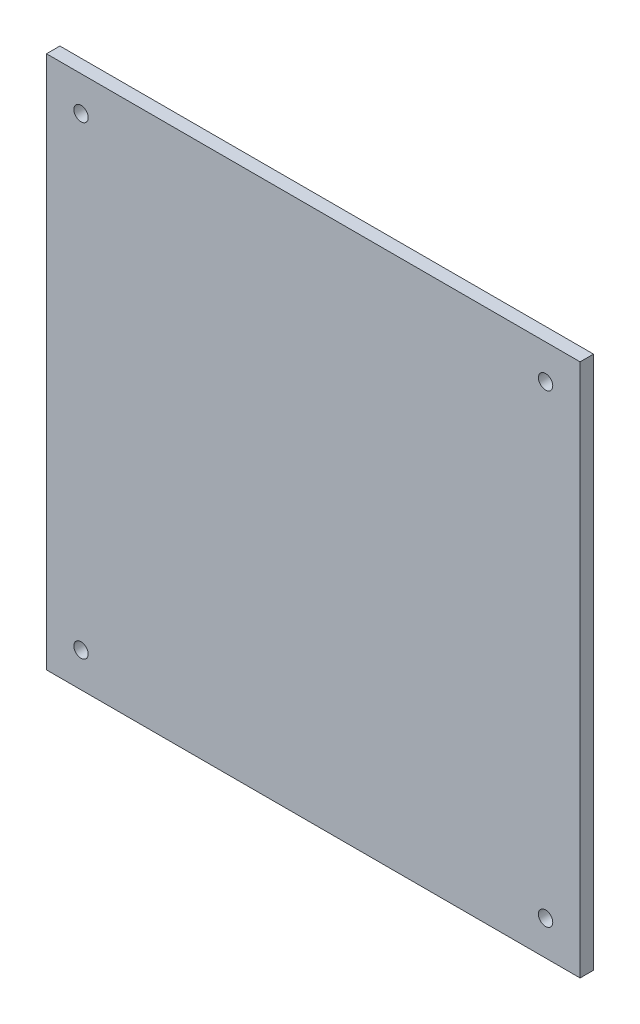
SolidWorks part; units mm, degrees
material "Acrylic (Medium-high impact)"
ref_plane "Front Plane" through (0, 0, 0) normal (0, 0, 1) x (1, 0, 0)
ref_plane "Top Plane" through (0, 0, 0) normal (0, 1, 0) x (1, 0, 0)
ref_plane "Right Plane" through (0, 0, 0) normal (1, 0, 0) x (0, 0, -1)
sketch "Sketch1" plane through (0, 0, 0) normal (0, 0, 1) x (1, 0, 0)
  line L1 (-63.175, -63.175) -> (63.175, -63.175)
  line L2 (-63.175, -63.175) -> (-63.175, 63.175)
  line L3 (-63.175, 63.175) -> (63.175, 63.175)
  line L4 (63.175, -63.175) -> (63.175, 63.175)
  line L5 (-63.175, -63.175) -> (63.175, 63.175) construction
  line L6 (-63.175, 63.175) -> (63.175, -63.175) construction
  point P0 (0, 0)
  dimension "D1" = 126.35
  dimension "D2" = 126.35
extrude "Boss-Extrude1" add sketch "Sketch1" along normal blind 3.175 contours L3 L4 L1 L2
extrude "Cut-Extrude2" cut sketch "Sketch3" against normal blind 3.175
sketch "Sketch3" plane through (-17.0478, -31.682, 3.175) normal (0, 0, 1) x (1, 0, 0)
  circle A5 centre (-37.9522, 86.682) radius 1.7
  circle A6 centre (-37.9522, -23.318) radius 1.7
  circle A7 centre (72.0478, -23.318) radius 1.7
  circle A8 centre (72.0478, 86.682) radius 1.7
